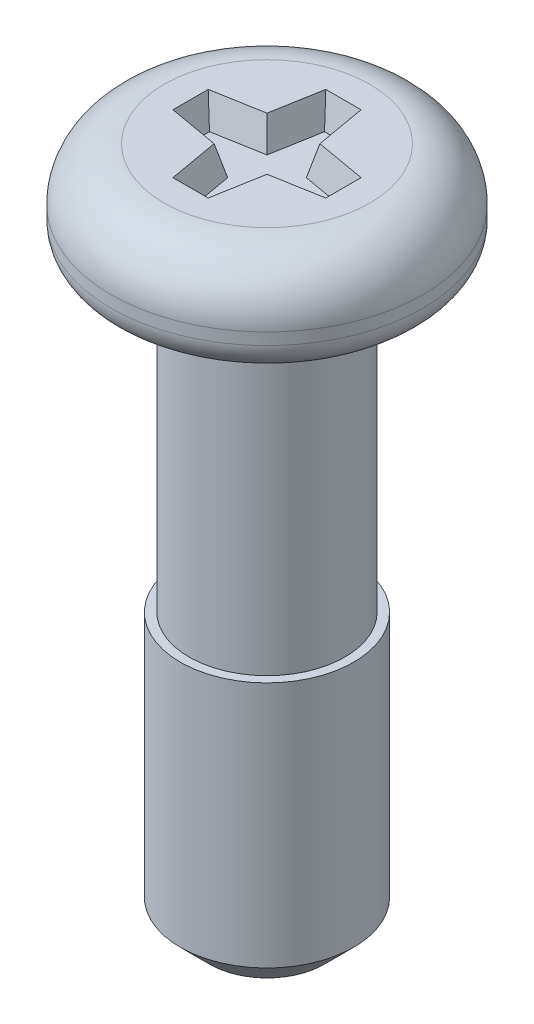
SolidWorks part; units mm, degrees
ref_plane "Front Plane" through (0, 0, 0) normal (0, 0, 1) x (1, 0, 0)
ref_plane "Top Plane" through (0, 0, 0) normal (0, 1, 0) x (1, 0, 0)
ref_plane "Right Plane" through (0, 0, 0) normal (1, 0, 0) x (0, 0, -1)
sketch "Sketch1" plane through (0, 0, 0) normal (0, 0, 1) x (1, 0, 0)
  line L0 (0, 0) -> (0, -11.6) construction
  line L1 (0, -11.6) -> (0.975, -11.6)
  line L2 (1.475, -11.1) -> (1.475, -6.9)
  line L3 (1.475, -1.6) -> (2.15, -1.6)
  line L4 (2.65, -1.1) -> (2.65, -0.9)
  line L5 (1.75, 0) -> (0, 0)
  line L6 (0, 0) -> (0, -11.6)
  line L7 (1.475, -11.1) -> (0.975, -11.6)
  line L8 (0, 0) -> (0, 1.913) construction
  line L9 (1.325, -6.9) -> (1.475, -6.9)
  line L10 (1.325, -6.9) -> (1.325, -1.75)
  arc A0 (2.65, -0.9) -> (1.75, 0) centre (1.75, -0.9) ccw
  arc A1 (2.15, -1.6) -> (2.65, -1.1) centre (2.15, -1.1) ccw
  arc A2 (1.325, -1.75) -> (1.475, -1.6) centre (1.475, -1.75) cw
  point P13 (1.475, -1.6)
  dimension "D3" = 0.9
  dimension "D6" = 0.5
  dimension "D7" = 0.15
  dimension "D8" = 135
  dimension "D4" = 0.5
  dimension "D10" = 2.65
  dimension "D1" = 5.3
  dimension "D2" = 1.6
  dimension "D5" = 2.95
  dimension "D9" = 10
  dimension "D11" = 5.3
revolve "Revolve1" add sketch "Sketch1" angle 360 about L0
cosmetic thread "Cosmetic Thread1" parameters "D1"=4.7, "D2"=1.95
sketch "Sketch2" plane through (0, 0, 0) normal (0, 1, 0) x (1, 0, 0)
  line L0 (0, 1.3) -> (0, 0) construction
  line L1 (0, 0) -> (1.3, 0) construction
  line L2 (-0.3001, 1.3) -> (0.3001, 1.3)
  line L3 (0.3001, 1.3) -> (0.45, 0.45)
  line L4 (0.45, 0.45) -> (1.3, 0.3001)
  line L5 (1.3, 0.3001) -> (1.3, -0.3001)
  line L6 (-1.3, 0.3001) -> (-1.3, -0.3001)
  line L7 (-0.45, 0.45) -> (-1.3, 0.3001)
  line L8 (-0.3001, 1.3) -> (-0.45, 0.45)
  line L9 (-0.45, -0.45) -> (-1.3, -0.3001)
  line L10 (-0.3001, -1.3) -> (-0.45, -0.45)
  line L11 (-0.3001, -1.3) -> (0.3001, -1.3)
  line L12 (0.3001, -1.3) -> (0.45, -0.45)
  line L13 (0.45, -0.45) -> (1.3, -0.3001)
  point P18 (-1.3, 0)
  point P26 (0, 0)
  dimension "D1" = 100
  dimension "D2" = 2.6
  dimension "D3" = 0.9
extrude "Cut-Extrude1" cut sketch "Sketch2" against normal blind 0.5 draft 15
